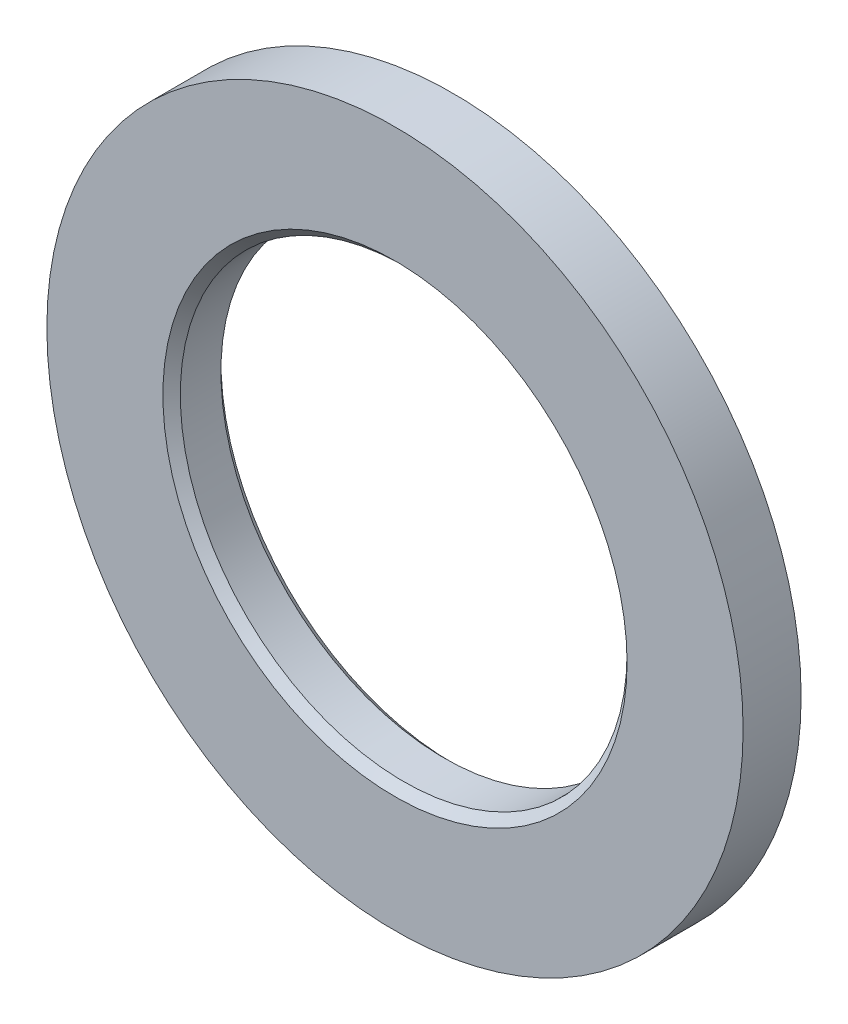
SolidWorks part; units mm, degrees
ref_plane "Front" through (0, 0, 0) normal (0, 0, 1) x (1, 0, 0)
ref_plane "Top" through (0, 0, 0) normal (0, 1, 0) x (1, 0, 0)
ref_plane "Right" through (0, 0, 0) normal (1, 0, 0) x (0, 0, -1)
sketch "Guard base" plane through (0, 0, 0) normal (0, 0, 1) x (1, 0, 0)
  circle A0 centre (0, 0) radius 30
  dimension "D1" = 60
extrude "Guard" add sketch "Guard base" along normal blind 5
sketch "Axle hole base" plane through (0, 0, 5) normal (0, 0, 1) x (1, 0, 0)
  circle A0 centre (0, 0) radius 19.25
  dimension "D1" = 38.5
extrude "Axle hole" cut sketch "Axle hole base" against normal through all
ref_axis "Center Z" through (0, 0, 0) along (0, 0, -1)
sketch "Mate ring room base" plane through (0, 0, 0) normal (0, 1, 0) x (1, 0, 0)
  line L0 (19.25, -5) -> (20, -5)
  line L1 (20, -5) -> (19.25, -4.25)
  line L2 (19.25, -4.25) -> (19.25, -5)
  line L5 (19.25, 0) -> (20, 0)
  line L6 (19.25, 0) -> (19.25, -0.75)
  line L7 (19.25, -0.75) -> (20, 0)
  dimension "D1" = 0.75
revolve "Mate ring room" cut sketch "Mate ring room base" angle 360 about axis through (0, 0, 0) along (0, 0, -1)
equation "\"mate_room\"= 0.25"
equation "\"removal_room\"= 0.75"
equation "\"large_inner_axle_diameter\"=20"
equation "\"D1@Axle hole base\"=\"39_92_spool_inner_diameter\"-\"spool_inner_diameter_room\"+\"mate_room\"*2"
equation "\"guard_thickness\"=5"
equation "\"spool_inner_diameter_room\"=1"
equation "\"D1@Guard\"=\"guard_thickness\""
equation "\"32_92_guard_diameter\"=50"
equation "\"D1@Guard base\"=\"39_92_guard_diameter\""
equation "\"32_92_spool_inner_diameter\"=32"
equation "\"32_92_spool_thickness\"=92"
equation "\"D1@Mate ring room base\" = \"removal_room\""
equation "\"bend_room_length_multiplier\"=3"
equation "\"small_inner_axle_diameter\"=17"
equation "\"32_92_extra_spool_thickness\"=-5"
equation "\"39_92_spool_inner_diameter\"=39"
equation "\"39_92_spool_thickness\"=92"
equation "\"39_92_guard_diameter\"=60"
equation "\"53_55_spool_inner_diameter\"=53"
equation "\"53_55_spool_thickness\"=55"
equation "\"53_55_guard_diameter\"=75"
equation "\"53_55_coupling_tooth_height\"=27"
equation "\"53_55_coupling_tooth_thickness_total\"=8"
equation "\"53_55_coupling_tooth_protrusion\"=1.5"
equation "\"53_55_coupling_tooth_head_height\"=7.5"
equation "\"53_55_coupling_tooth_depth\"=10"
equation "\"53_55_coupling_tooth_base_thickness\"=9.5"
